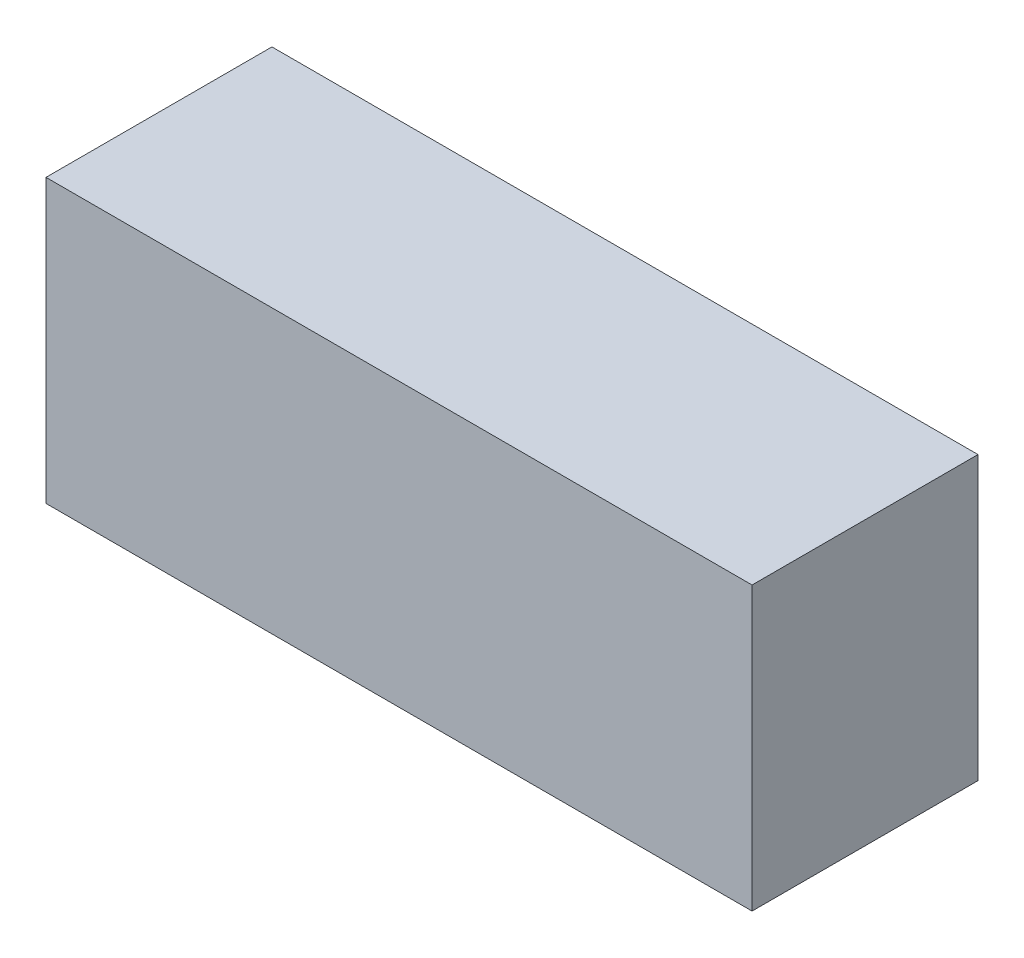
SolidWorks part; units mm, degrees
ref_plane "Front Plane" through (0, 0, 0) normal (0, 0, 1) x (1, 0, 0)
ref_plane "Top Plane" through (0, 0, 0) normal (0, 1, 0) x (1, 0, 0)
ref_plane "Right Plane" through (0, 0, 0) normal (1, 0, 0) x (0, 0, -1)
sketch "Sketch1" plane through (0, 0, 0) normal (0, 0, 1) x (1, 0, 0)
  line L1 (-50, -20) -> (50, -20)
  line L2 (-50, -20) -> (-50, 20)
  line L3 (-50, 20) -> (50, 20)
  line L4 (50, -20) -> (50, 20)
  line L5 (-50, -20) -> (50, 20) construction
  line L6 (-50, 20) -> (50, -20) construction
  point P0 (0, 0)
  dimension "D1" = 100
  dimension "D2" = 40
extrude "Boss-Extrude1" add sketch "Sketch1" along normal blind 32 contours L3 L4 L1 L2
